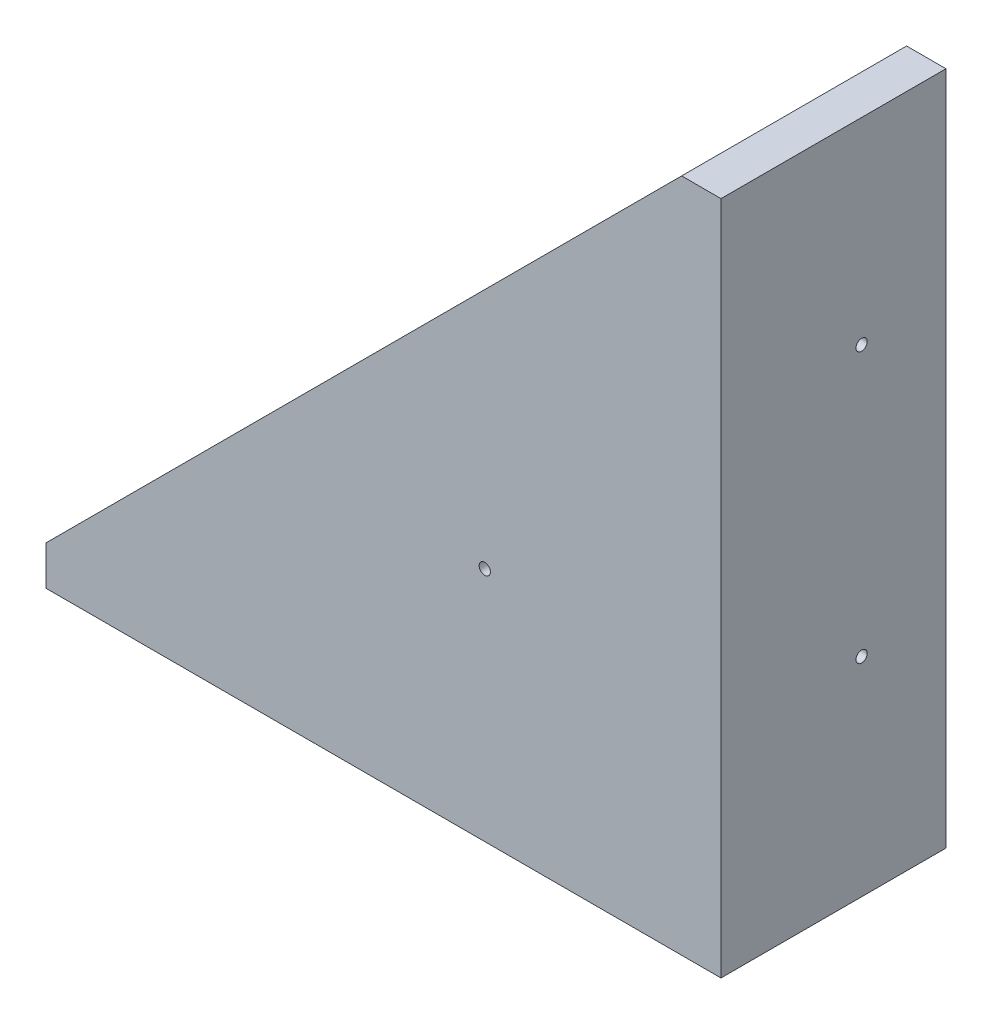
SolidWorks part; units mm, degrees
ref_plane "Plan de face" through (0, 0, 0) normal (0, 0, 1) x (1, 0, 0)
ref_plane "Plan de dessus" through (0, 0, 0) normal (0, 1, 0) x (1, 0, 0)
ref_plane "Plan de droite" through (0, 0, 0) normal (1, 0, 0) x (0, 0, -1)
sketch "Esquisse1" plane through (0, 0, 0) normal (0, 0, 1) x (1, 0, 0)
  line L1 (-92.7425, 3.3367) -> (27.2575, 3.3367)
  line L2 (-92.7425, 3.3367) -> (-92.7425, -3.6633)
  line L3 (-92.7425, -3.6633) -> (27.2575, -3.6633)
  line L4 (27.2575, 3.3367) -> (27.2575, -3.6633)
  line L5 (27.2575, 3.3367) -> (20.2575, 3.3367)
  line L6 (27.2575, 3.3367) -> (27.2575, 116.3367)
  line L7 (27.2575, 116.3367) -> (20.2575, 116.3367)
  line L8 (20.2575, 3.3367) -> (20.2575, 116.3367)
  dimension "D1" = 7
  dimension "D2" = 120
  dimension "D3" = 113
  dimension "D4" = 7
extrude "Boss.-Extru.2" add sketch "Esquisse1" along normal blind 40 contours L8 L1 L6 L7 | L4 L1 L2 L3
sketch "Esquisse2" plane through (0, 3.3367, 0) normal (0, 1, 0) x (1, 0, 0)
  line L1 (-92.7425, 0) -> (20.2575, 0) construction
  line L2 (-92.7425, -40) -> (-92.7425, 0) construction
  circle A0 centre (-57.7425, -15) radius 1
  dimension "D1" = 2
  dimension "D2" = 15
  dimension "D3" = 35
sketch "Esquisse4" plane through (0, 3.3367, 0) normal (0, 1, 0) x (1, 0, 0)
  line L0 (20.2575, -40) -> (20.2575, 0) construction
  line L1 (20.2575, -40) -> (-92.7425, -40)
  line L2 (20.2575, -40) -> (20.2575, -30)
  line L3 (20.2575, -30) -> (-92.7425, -30)
  line L4 (-92.7425, -40) -> (-92.7425, -30)
  line L6 (-92.7425, -40) -> (20.2575, -40) construction
  line L7 (-92.7425, -40) -> (-92.7425, 0) construction
  dimension "D1" = 10
  dimension "D2" = 0
  dimension "D3" = 0
extrude "Boss.-Extru.8" add sketch "Esquisse4" along normal blind 115
sketch "Esquisse6" plane through (0, 0, 40) normal (0, 0, 1) x (1, 0, 0)
  line L0 (20.2575, 116.3367) -> (-92.7425, 3.3367)
  line L1 (20.2575, 116.3367) -> (20.2575, 118.3367)
  line L2 (20.2575, 118.3367) -> (-92.7425, 118.3367)
  line L3 (-92.7425, 118.3367) -> (-92.7425, 3.3367)
extrude "Enlèv. mat.-Extru.2" cut sketch "Esquisse6" against normal blind 115
extrude "Enlèv. mat.-Extru.4" cut sketch "Esquisse2" against normal blind 115
sketch "Esquisse7" plane through (0, 3.3367, 0) normal (0, 1, 0) x (1, 0, 0)
  line L0 (-92.7425, 0) -> (20.2575, 0) construction
  line L1 (20.2575, -30) -> (20.2575, 0) construction
  circle A0 centre (-9.7425, -15) radius 1
  dimension "D1" = 2
  dimension "D2" = 15
  dimension "D3" = 30
extrude "Enlèv. mat.-Extru.5" cut sketch "Esquisse7" against normal blind 115
sketch "Esquisse8" plane through (20.2575, 0, 0) normal (-1, 0, 0) x (0, 0, 1)
  line L0 (30, 116.3367) -> (0, 116.3367) construction
  line L1 (0, 3.3367) -> (0, 116.3367) construction
  circle A0 centre (15, 81.3367) radius 1
  dimension "D1" = 2
  dimension "D2" = 35
  dimension "D3" = 15
extrude "Enlèv. mat.-Extru.6" cut sketch "Esquisse8" against normal blind 115
sketch "Esquisse9" plane through (20.2575, 0, 0) normal (-1, 0, 0) x (0, 0, 1)
  line L0 (0, 3.3367) -> (0, 116.3367) construction
  line L1 (30, 3.3367) -> (0, 3.3367) construction
  circle A0 centre (15, 33.3367) radius 1
  dimension "D1" = 2
  dimension "D2" = 15
  dimension "D3" = 30
extrude "Enlèv. mat.-Extru.7" cut sketch "Esquisse9" against normal blind 115
sketch "Esquisse10" plane through (0, 0, 30) normal (0, 0, -1) x (-1, 0, 0)
  line L0 (-20.2575, 3.3367) -> (92.7425, 3.3367) construction
  line L1 (-20.2575, 116.3367) -> (-20.2575, 3.3367) construction
  circle A0 centre (14.7425, 38.3367) radius 1
  dimension "D1" = 2
  dimension "D2" = 35
  dimension "D3" = 35
extrude "Enlèv. mat.-Extru.8" cut sketch "Esquisse10" against normal blind 20
